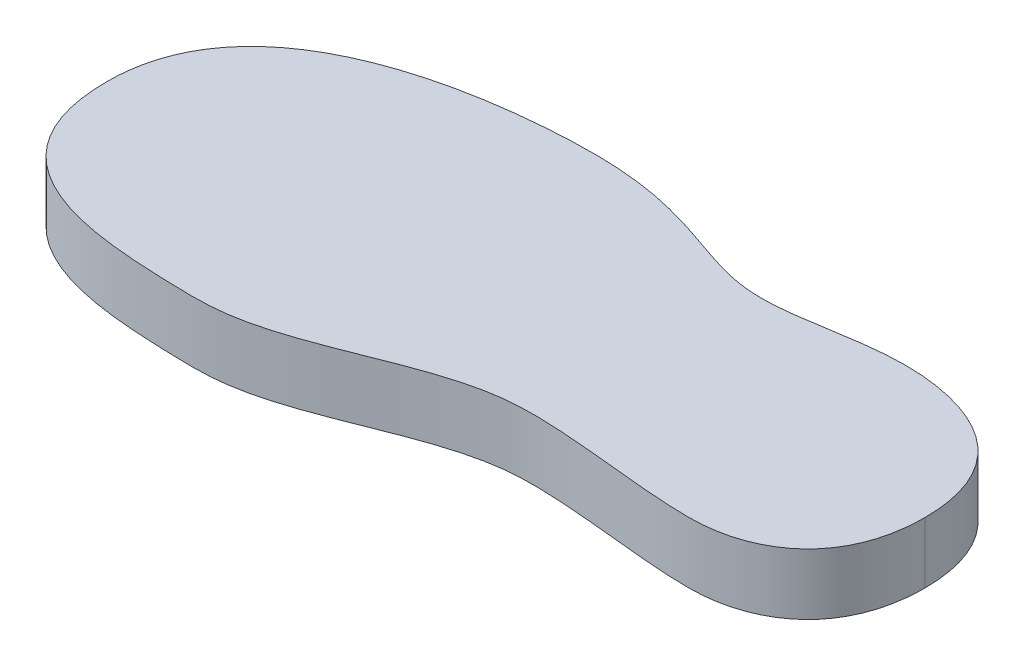
SolidWorks part; units mm, degrees
ref_plane "Front Plane" through (0, 0, 0) normal (0, 0, 1) x (1, 0, 0)
ref_plane "Top Plane" through (0, 0, 0) normal (0, 1, 0) x (1, 0, 0)
ref_plane "Right Plane" through (0, 0, 0) normal (1, 0, 0) x (0, 0, -1)
sketch "Sketch1" plane through (0, 0, 0) normal (0, 1, 0) x (1, 0, 0)
  line L0 (0, 0) -> (0, 15.15) construction
  line L1 (0, 15.15) -> (-100.9, 15.15) construction
  line L2 (-100.9, 15.15) -> (-100.9, -15.15) construction
  line L3 (-100.9, -15.15) -> (10.4, -15.15) construction
  line L4 (10.4, -15.15) -> (10.4, 15.15) construction
  line L5 (10.4, 15.15) -> (0, 15.15) construction
  line L6 (0, 0) -> (10.4, 0) construction
  line L7 (0, 0) -> (-100.9, 0) construction
  line L8 (-3.6, 0) -> (-3.6, 20) construction
  line L9 (10.4, 0) -> (19.6, 0) construction
  line L10 (-59.2, 0) -> (-59.2, 24.5) construction
  line L11 (-64.1, 0) -> (-64.1, 15.15) construction
  line L12 (-64.1, 0) -> (-64.1, -5.1) construction
  line L13 (-64.1, -5.1) -> (-109.1, -5.1) construction
  line L14 (-24.8, 0) -> (-24.8, 17.7) construction
  dimension "D1" = 30.3
  dimension "D2" = 111.3
  dimension "D3" = 10.4
  dimension "D4" = 3.6
  dimension "D5" = 20
  dimension "D6" = 19.6
  dimension "D7" = 24.8
  dimension "D8" = 5.1
  dimension "D9" = 45
  dimension "D10" = 64.1
  dimension "D11" = 24.5
  dimension "D12" = 59.2
  dimension "D13" = 17.7
sketch "Sketch3" plane through (0, 0, 0) normal (0, 1, 0) x (1, 0, 0)
  line L0 (0, 0) -> (0, -19.3) construction
  line L1 (-27.1, 0) -> (-27.1, -17.4) construction
  line L2 (0, 0) -> (-100.9, 0) construction
  line L3 (-72, 0) -> (-72, -28.6) construction
  dimension "D1" = 19.3
  dimension "D2" = 17.4
  dimension "D3" = 28.6
  dimension "D4" = 27.1
  dimension "D5" = 72
sketch "Sketch2" plane through (0, 0, 0) normal (0, 1, 0) x (1, 0, 0)
  line L0 (19.6, -11.1333) -> (19.6, 11.1333) construction
  line L1 (-82.9362, -28.6) -> (-59.2746, -28.6) construction
  line L2 (-109.1, 12.0166) -> (-109.1, -22.4526) construction
  line L3 (-38.3758, -17.4) -> (-20.5335, -17.4) construction
  line L4 (-6.8012, -19.3) -> (7.7138, -19.3) construction
  line L5 (-44.6362, 24.5) -> (-71.0994, 24.5) construction
  line L6 (-20.2625, 17.7) -> (-32.3488, 17.7) construction
  line L7 (5.0808, 20) -> (-8.6275, 20) construction
  line L8 (19.6, -12.7653) -> (19.6, 13.2246) construction
  line L9 (-109.1, 13.3599) -> (-109.1, -24.097) construction
  spline S0 degree 3 poles (-109.1, -5.1) (-109.1, 18.3106) (-73.8094, 24.6958) (-43.0009, 24.4074) (-34.22, 17.8388) (-19.7452, 17.5626) (-9.8315, 20.0891) (7.1736, 19.9358) (19.6, 14.2893) (19.6, 0) knots 0 0 0 0 0.230584 0.286176 0.525951 0.574149 0.719962 0.76437 1 1 1 1
  spline S1 degree 3 poles (19.6, 0) (19.6, -12.7982) (9.6283, -19.5586) (-8.5374, -19.1352) (-19.7964, -17.3572) (-41.2186, -17.3729) (-58.114, -28.9795) (-85.1554, -28.3277) (-109.1, -26.6433) (-109.1, -5.1) knots 0 0 0 0 0.17462 0.213185 0.36648 0.418282 0.679408 0.740843 1 1 1 1
  point P0 (-59.2, 24.5)
  point P2 (-3.6, 20)
  point P4 (19.6, 0)
  point P6 (-109.1, -5.1)
  point P8 (-24.8, 17.7)
extrude "Boss-Extrude1" add sketch "Sketch2" along normal blind 10
